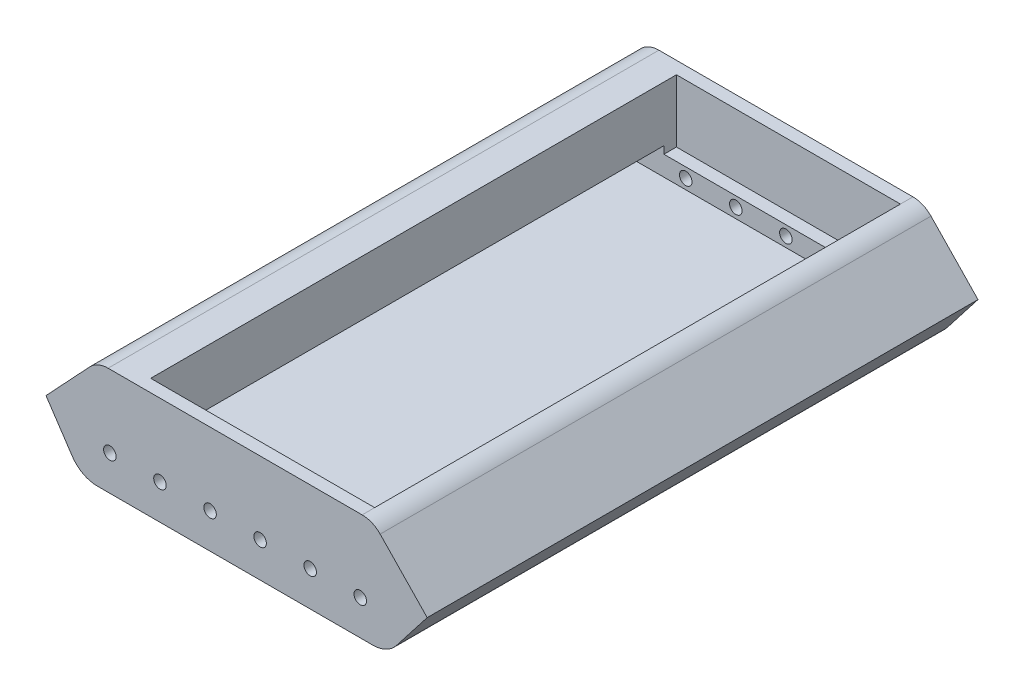
SolidWorks part; units mm, degrees
ref_plane "Front Plane" through (0, 0, 0) normal (0, 0, 1) x (1, 0, 0)
ref_plane "Top Plane" through (0, 0, 0) normal (0, 1, 0) x (1, 0, 0)
ref_plane "Right Plane" through (0, 0, 0) normal (1, 0, 0) x (0, 0, -1)
sketch "Sketch1" plane through (0, 0, 0) normal (0, 0, 1) x (1, 0, 0)
  line L0 (-3.3625, 0) -> (-109.8474, 0)
  line L1 (-115.3944, -1.6795) -> (-120.2303, -4.9034)
  line L2 (-120.2303, -4.9034) -> (-113.4689, -15.0454)
  line L3 (-111.8048, -15.936) -> (-1.7523, -15.936)
  line L4 (-0.1737, -15.164) -> (7.3106, -5.5431)
  line L5 (7.3106, -5.5431) -> (2.6794, -2.0316)
  arc A0 (-115.3944, -1.6795) -> (-109.8474, 0) centre (-109.8474, -10) cw
  arc A1 (2.6794, -2.0316) -> (-3.3625, 0) centre (-3.3625, -10) ccw
  arc A2 (-1.7523, -15.936) -> (-0.1737, -15.164) centre (-1.7523, -13.936) ccw
  arc A3 (-111.8048, -15.936) -> (-113.4689, -15.0454) centre (-111.8048, -13.936) cw
  point P9 (-112.8752, 0)
  point P12 (0, 0)
  point P17 (-112.8752, -15.936)
  dimension "D1" = 10
  dimension "D2" = 10
  dimension "D3" = 2
extrude "Extrude-Thin1" add sketch "Sketch1" along normal blind 220 thin
sketch "Sketch3" plane through (0, 0, 220) normal (0, 0, 1) x (1, 0, 0)
  line L0 (-120.2303, -4.9034) -> (7.3106, -5.5431)
  line L1 (7.3106, -5.5431) -> (7.3106, -21.8014)
  line L2 (7.3106, -21.8014) -> (-120.5254, -22.1792)
  line L3 (-120.5254, -22.1792) -> (-120.2303, -4.9034)
  arc A0 (-1.7523, -25.936) -> (7.7193, -21.3041) centre (-1.7523, -13.936) ccw construction
  arc A1 (-121.7894, -20.5924) -> (-111.8048, -25.936) centre (-111.8048, -13.936) ccw construction
extrude "Boss-Extrude1" add sketch "Sketch3" against normal blind 10
sketch "Sketch4" plane through (0, 0, 0) normal (0, 0, -1) x (-1, 0, 0)
  line L0 (-7.3106, -5.5431) -> (120.2303, -4.9034)
  line L1 (120.2303, -4.9034) -> (120.2303, -22.4807)
  line L2 (120.2303, -22.4807) -> (-5.2889, -22.4807)
  line L3 (-7.2354, -20.5342) -> (-7.3106, -5.5431)
  line L4 (-7.2354, -20.5342) -> (-5.2889, -22.4807)
  arc A0 (111.8048, -25.936) -> (121.7894, -20.5924) centre (111.8048, -13.936) ccw construction
extrude "Boss-Extrude2" add sketch "Sketch4" against normal blind 10
sketch "Sketch5" plane through (0, 0, 0) normal (0, 0, -1) x (-1, 0, 0)
  line L0 (-7.3106, -5.5431) -> (-30.0904, -5.5431)
  line L1 (-30.0904, -5.5431) -> (-30.0904, 22.1601)
  line L2 (-30.0904, 22.1601) -> (140.4611, 22.1601)
  line L3 (140.4611, 22.1601) -> (140.4611, -4.8446)
  line L4 (140.4611, -4.8446) -> (120.2303, -4.9034)
  line L5 (120.2303, -4.9034) -> (-7.3106, -5.5431)
extrude "Cut-Extrude1" cut sketch "Sketch5" against normal through all
sketch "Sketch6" plane through (0, 0, 220) normal (0, 0, 1) x (1, 0, 0)
  line L1 (7.3106, -5.5431) -> (-120.2303, -4.9034) construction
  circle A0 centre (-106.7523, -11.9727) radius 2.5
  circle A1 centre (-6.7523, -11.9727) radius 2.5
  circle A2 centre (-86.7523, -11.9727) radius 2.5
  circle A3 centre (-66.7523, -11.9727) radius 2.5
  circle A4 centre (-46.7523, -11.9727) radius 2.5
  circle A5 centre (-26.7523, -11.9727) radius 2.5
  dimension "D1" = 5
  dimension "D3" = 5
  dimension "D2" = 20
  dimension "D4" = 6.5
  dimension "D5" = 5
extrude "Cut-Extrude3" cut sketch "Sketch6" against normal through all
sketch "Sketch8" plane through (0, 0, 220) normal (0, 0, 1) x (1, 0, 0)
  line L1 (-107.4672, 17.0021) -> (-6.0024, 17.0021)
  line L2 (1.1973, 13.9422) -> (19.9801, -5.5431)
  line L3 (-114.7687, 13.8351) -> (-132.2721, -4.8684)
  line L9 (7.7193, -21.3041) -> (19.9801, -5.5431)
  line L10 (19.9801, -5.5431) -> (7.3106, -5.5431)
  line L11 (7.3106, -5.5431) -> (-120.2303, -4.9034)
  line L12 (-120.2303, -4.9034) -> (-132.2721, -4.8684)
  line L13 (-132.2721, -4.8684) -> (-121.7894, -20.5924)
  line L14 (-111.8048, -25.936) -> (-1.7523, -25.936)
  line L16 (19.9801, -5.5431) -> (7.3106, -5.5431)
  line L17 (7.3106, -5.5431) -> (-120.2303, -4.9034)
  line L18 (-120.2303, -4.9034) -> (-132.2721, -4.8684)
  arc A0 (-6.0024, 17.0021) -> (1.1973, 13.9422) centre (-6.0024, 7.0021) cw
  arc A1 (-114.7687, 13.8351) -> (-107.4672, 17.0021) centre (-107.4672, 7.0021) cw
  arc A4 (-121.7894, -20.5924) -> (-111.8048, -25.936) centre (-111.8048, -13.936) ccw
  arc A5 (-1.7523, -25.936) -> (7.7193, -21.3041) centre (-1.7523, -13.936) ccw
  dimension "D1" = 10
  dimension "D2" = 0
extrude "Boss-Extrude3" add sketch "Sketch8" against normal up to vertex (220 mm away)
sketch "Sketch9" plane through (0, 17.0021, 0) normal (0, 1, 0) x (1, 0, 0)
  line L0 (-6.0024, 0) -> (-6.0024, -220) construction
  line L1 (-95.4672, -5) -> (-6.0024, -5)
  line L2 (-95.4672, -5) -> (-95.4672, -215)
  line L3 (-95.4672, -215) -> (-6.0024, -215)
  line L4 (-6.0024, -5) -> (-6.0024, -215)
  line L5 (-6.0024, 0) -> (-107.4672, 0) construction
  line L6 (-6.0024, -220) -> (-107.4672, -220) construction
  line L7 (-107.4672, 0) -> (-107.4672, -220) construction
  dimension "D1" = 5
  dimension "D2" = 5
  dimension "D3" = 12
extrude "Cut-Extrude5" cut sketch "Sketch9" against normal blind 25
sketch "Sketch10" plane through (-68.0862, 63.7179, 0) normal (-0.7301, 0.6833, 0) x (0, 0, 1)
  line L0 (0, -68.3195) -> (220, -68.3195) construction
  line L1 (90.7461, -74.3195) -> (129.2539, -74.3195)
  line L2 (90.7461, -74.3195) -> (90.7461, -89.9357)
  line L3 (90.7461, -89.9357) -> (129.2539, -89.9357)
  line L4 (129.2539, -74.3195) -> (129.2539, -89.9357)
  line L5 (220, -93.9357) -> (0, -93.9357) construction
  line L6 (220, -68.3195) -> (220, -93.9357) construction
  point P8 (110, -74.3195)
  dimension "D1" = 6
  dimension "D2" = 4
  dimension "D3" = 110
extrude "Cut-Extrude6" cut sketch "Sketch10" against normal blind 20
